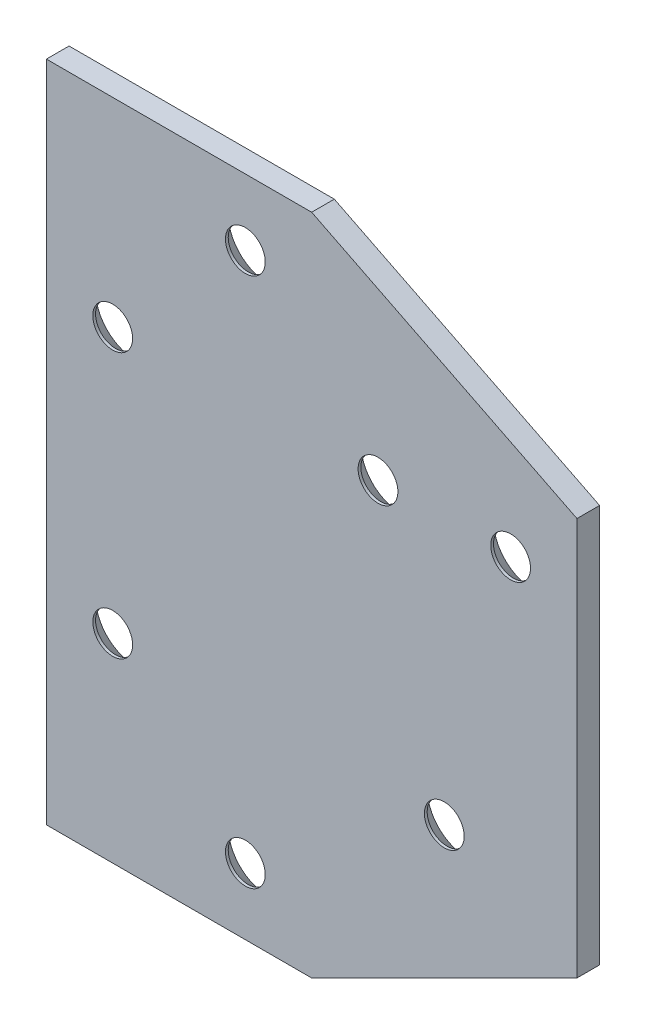
SolidWorks part; units mm, degrees
material "AISI 1010 Steel, hot rolled bar"
ref_plane "Front Plane" through (0, 0, 0) normal (0, 0, 1) x (1, 0, 0)
ref_plane "Top Plane" through (0, 0, 0) normal (0, 1, 0) x (1, 0, 0)
ref_plane "Right Plane" through (0, 0, 0) normal (1, 0, 0) x (0, 0, -1)
sketch "Sketch1" plane through (0, 0, 0) normal (0, 0, 1) x (1, 0, 0)
  line L0 (0, 0) -> (40, 0) construction
  line L1 (-20, -50) -> (20, -50)
  line L2 (-20, -50) -> (-20, 50)
  line L3 (-20, 50) -> (20, 50)
  line L4 (20, -50) -> (20, 50) construction
  line L5 (-20, -50) -> (20, 50) construction
  line L6 (-20, 50) -> (20, -50) construction
  line L7 (20, 50) -> (60, 30)
  line L8 (60, -30) -> (20, -30) construction
  line L9 (60, -30) -> (60, 30)
  line L10 (60, 30) -> (20, 30) construction
  line L11 (20, -30) -> (20, 30) construction
  line L12 (60, -30) -> (20, 30) construction
  line L13 (60, 30) -> (20, -30) construction
  line L14 (60, -30) -> (20, -50)
  point P0 (0, 0)
  dimension "D1" = 40
  dimension "D2" = 100
  dimension "D3" = 40
  dimension "D4" = 60
extrude "Boss-Extrude1" add sketch "Sketch1" along normal blind 3.416 contours L3 L7 L9 L14 L1 L2
sketch "Sketch2" plane through (0, 0, 3.416) normal (0, 0, 1) x (1, 0, 0)
  line L0 (-20, 0) -> (-10, 0) construction
  line L1 (-10, 0) -> (-10, 20) construction
  line L2 (10, 20) -> (30, 20) construction
  line L3 (-10, 20) -> (10, 20) construction
  line L4 (-10, 20) -> (-10, 40) construction
  line L5 (-10, 40) -> (10, 40) construction
  line L6 (-20, 50) -> (-20, -50)
  line L7 (-20, -50) -> (20, -50)
  line L8 (20, -50) -> (60, -30)
  line L9 (60, -30) -> (60, 30)
  line L10 (60, 30) -> (20, 50)
  line L11 (20, 50) -> (-20, 50)
  line L12 (-20, 50) -> (-20, -50) construction
  line L13 (-20, -50) -> (20, -50) construction
  line L14 (20, -50) -> (60, -30) construction
  line L15 (60, -30) -> (60, 30) construction
  line L16 (60, 30) -> (20, 50) construction
  line L17 (20, 50) -> (-20, 50) construction
  line L18 (10, 20) -> (10, 40) construction
  line L19 (0, 40) -> (0, 20) construction
  line L20 (-10, 30) -> (10, 30) construction
  line L21 (30, 20) -> (50, 20) construction
  line L22 (-10, -20) -> (40, -20) construction
  circle A0 centre (-10, 20) radius 3
  circle A1 centre (10, 40) radius 3
  circle A2 centre (30, 20) radius 3
  circle A3 centre (50, 20) radius 3
  circle A4 centre (-10, -20) radius 3
  circle A5 centre (10, -40) radius 3
  circle A6 centre (40, -20) radius 3
  point P12 (-10, 0)
  point P187 (0, 30)
  dimension "D8" = 6
  dimension "D2" = 10
  dimension "D3" = 20
  dimension "D4" = 20
  dimension "D5" = 20
  dimension "D6" = 20
  dimension "D7" = 20
  dimension "D9" = 50
  dimension "D1" = 0
extrude "Cut-Extrude1" cut sketch "Sketch2" against normal through all
chamfer "Chamfer1" distance 3 angle 45 7 edges at (-13, -20, 0) (7, -40, 0) (43, -20, 0) (-7, 20, 0) (13, 40, 0) (33, 20, 0) (53, 20, 0)
fillet "Fillet1" [suppressed] radius 1
